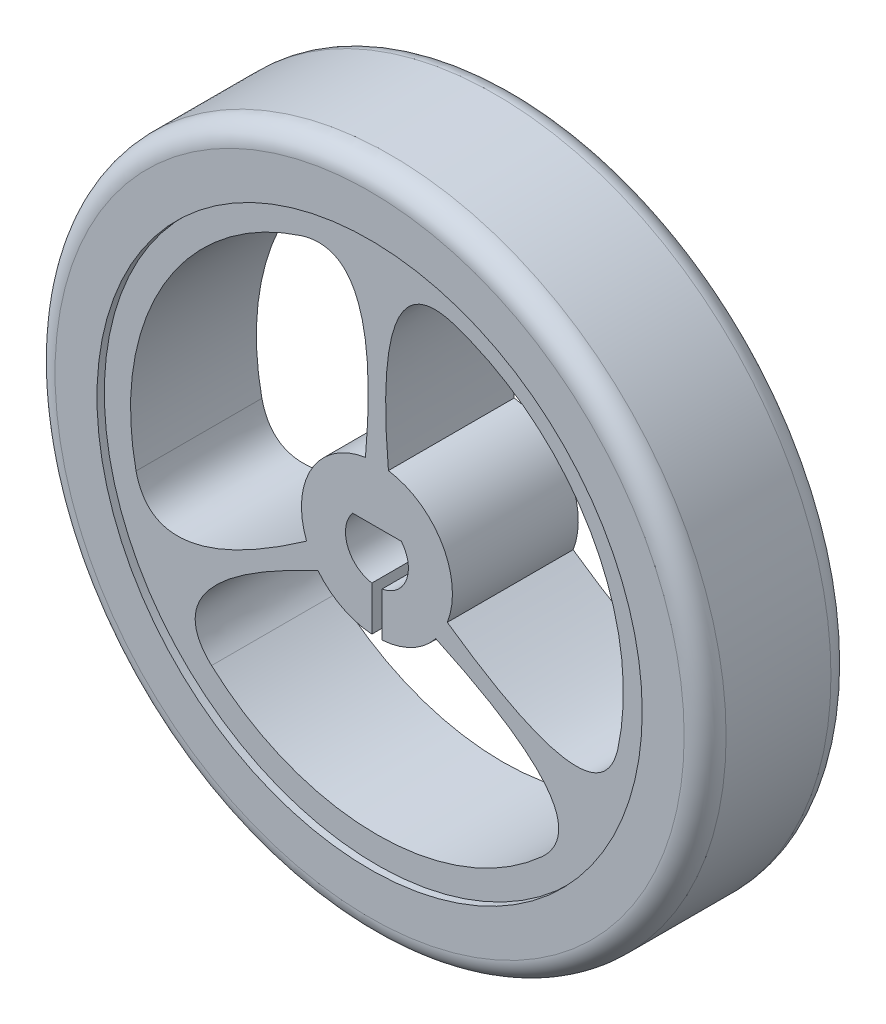
SolidWorks part; units mm, degrees
ref_plane "Ön Düzlem" through (0, 0, 0) normal (0, 0, 1) x (1, 0, 0)
ref_plane "Üst Düzlem" through (0, 0, 0) normal (0, 1, 0) x (1, 0, 0)
ref_plane "Sağ Düzlem" through (0, 0, 0) normal (1, 0, 0) x (0, 0, -1)
sketch "Çizim1" plane through (0, 0, 0) normal (0, 0, 1) x (1, 0, 0)
  circle A0 centre (0, 0) radius 14.3
extrude "Yükseklik-Ekstrüzyon2" add sketch "Çizim1" along normal blind 3
sketch "Çizim2" plane through (0, 0, 3) normal (0, 0, 1) x (1, 0, 0)
  circle A1 centre (0, 0) radius 13
extrude "Yükseklik-Ekstrüzyon3" add sketch "Çizim2" along normal blind 1.5
sketch "Çizim3" plane through (0, 0, 0) normal (0, 0, -1) x (-1, 0, 0)
  circle A0 centre (0, 0) radius 13
extrude "Yükseklik-Ekstrüzyon4" add sketch "Çizim3" along normal blind 1.5
sketch "Çizim4" plane through (0, 0, 4.5) normal (0, 0, 1) x (1, 0, 0)
  arc A0 (-3.6, 11.1849) -> (-11.4864, -2.4748) centre (0, 0) ccw
  arc A1 (-0.5473, 3.5581) -> (-3.3551, -1.3051) centre (0, 0) ccw
  arc A3 (11.4864, -2.4748) -> (3.6, 11.1849) centre (0, 0) ccw
  arc A4 (3.3551, -1.3051) -> (0.5473, 3.5581) centre (0, 0) ccw
  arc A5 (-7.8864, -8.7102) -> (7.8864, -8.7102) centre (0, 0) ccw
  arc A6 (-2.8078, -2.2531) -> (2.8078, -2.2531) centre (0, 0) ccw
  arc A7 (-3.6, 11.1849) -> (-11.4864, -2.4748) centre (0, 0) ccw
  arc A8 (-0.5473, 3.5581) -> (-3.3551, -1.3051) centre (0, 0) ccw
  arc A9 (-2.8078, -2.2531) -> (2.8078, -2.2531) centre (0, 0) ccw
  arc A10 (-7.8864, -8.7102) -> (7.8864, -8.7102) centre (0, 0) ccw
  spline S0 degree 2 poles (0.5473, 3.5581) (-0.2555, 12.5863) (3.8151, 11.1134) knots 0 0 0 1 1 1
  spline S1 degree 2 poles (3.3551, -1.3051) (10.7723, -6.5144) (11.532, -2.2527) knots 0 0 0 1 1 1
  spline S2 degree 2 poles (2.8078, -2.2531) (11.0278, -6.0719) (7.7169, -8.8607) knots 0 0 0 1 1 1
  spline S3 degree 2 poles (-2.8078, -2.2531) (-11.0278, -6.0719) (-7.7169, -8.8607) knots 0 0 0 1 1 1
  spline S4 degree 2 poles (-3.3551, -1.3051) (-10.7723, -6.5144) (-11.532, -2.2527) knots 0 0 0 1 1 1
  spline S5 degree 2 poles (-0.5473, 3.5581) (0.2555, 12.5863) (-3.8151, 11.1134) knots 0 0 0 1 1 1
  point P39 (0, 0)
  dimension "D4" = 3
extrude "Kes-Ekstrüzyon1" cut sketch "Çizim4" against normal blind 7 contours A1 S5 A0 A7 S4 A8 | A4 S1 A3 S0 | A6 S3 A5 A10 S2
sketch "Çizim5" plane through (0, 0, 4.5) normal (0, 0, 1) x (1, 0, 0)
  line L0 (-0.2433, -3.5918) -> (-0.2433, -3.7048)
  line L1 (-0.2433, -1.4801) -> (-0.2433, -3.5918)
  line L2 (0.2468, -1.4796) -> (0.2468, -3.5918)
  line L3 (-1.1621, 0.9484) -> (1.1621, 0.9484)
  line L4 (-0.2433, -3.7048) -> (0.2468, -3.7048)
  line L5 (0.2468, -3.7048) -> (0.2468, -3.5918)
  arc A0 (-1.1621, 0.9484) -> (-0.2433, -1.4801) centre (0, 0) ccw
  arc A1 (-2.8078, -2.2531) -> (2.8078, -2.2531) centre (0, 0) ccw construction
  arc A2 (0.2468, -1.4796) -> (1.1621, 0.9484) centre (0, 0) ccw
extrude "Kes-Ekstrüzyon3" cut sketch "Çizim5" against normal blind 7
sketch "Çizim6" plane through (0, 0, 4.5) normal (0, 0, 1) x (1, 0, 0)
  circle A0 centre (0, 0) radius 16
  circle A1 centre (0, 0) radius 13
extrude "Yükseklik-Ekstrüzyon5" add sketch "Çizim6" against normal blind 6.65 and the other way blind 0.35
fillet "Radyus1" radius 1 1 edges at (16, 0, 4.85)
fillet "Radyus2" radius 1 1 edges at (16, 0, -2.15)
